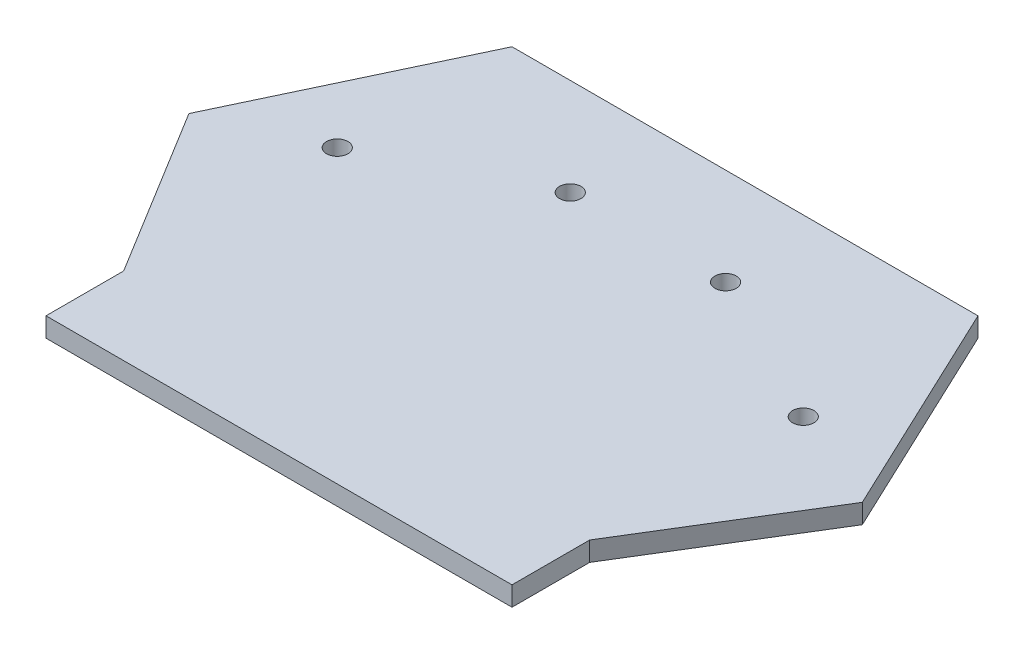
SolidWorks part; units mm, degrees
ref_plane "Front Plane" through (0, 0, 0) normal (0, 0, 1) x (1, 0, 0)
ref_plane "Top Plane" through (0, 0, 0) normal (0, 1, 0) x (1, 0, 0)
ref_plane "Right Plane" through (0, 0, 0) normal (1, 0, 0) x (0, 0, -1)
sketch "Sketch2" plane through (0, 0, 0) normal (0, 1, 0) x (1, 0, 0)
  line L0 (0, 0) -> (0, 30)
  line L1 (60, 30) -> (-60, 30)
  line L2 (0, 30) -> (0, 130)
  line L3 (-60, 30) -> (-60, 10)
  line L4 (20, 130) -> (-20, 130)
  line L5 (60, 130) -> (-60, 130)
  line L6 (-60, 10) -> (60, 10)
  line L7 (86.701, 73.5057) -> (60, 30)
  line L8 (86.701, 73.5057) -> (60, 130)
  line L9 (60, 30) -> (60, 10)
  line L10 (-86.701, 73.5057) -> (-60, 130)
  line L11 (-86.701, 73.5057) -> (-60, 30)
  circle A0 centre (-20, 105) radius 2.75
  circle A1 centre (-60, 85) radius 2.75
  circle A2 centre (60, 85) radius 2.75
  circle A3 centre (20, 105) radius 2.75
  point P22 (0, 10)
extrude "Boss-Extrude1" add sketch "Sketch2" along normal blind 5 contours L10 L11 L1 L2 L4 L5 A1 A0 | L7 L8 L5 L4 L2 L1 A2 A3 | L3 L6 L0 L1 | L9 L1 L0 L6
